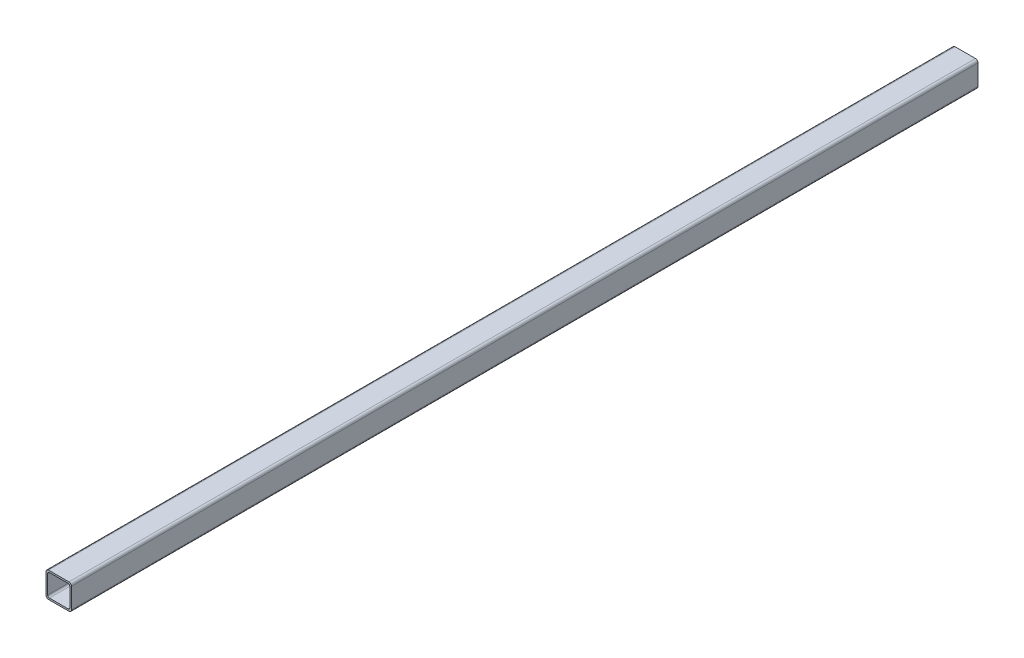
SolidWorks part; units mm, degrees
material "AISI 1020"
ref_plane "Спереди" through (0, 0, 0) normal (0, 0, 1) x (1, 0, 0)
ref_plane "Сверху" through (0, 0, 0) normal (0, 1, 0) x (1, 0, 0)
ref_plane "Справа" through (0, 0, 0) normal (1, 0, 0) x (0, 0, -1)
ref_plane "Плоскость1" through (0, 0, -10) normal (0, 0, 1) x (1, 0, 0)
sketch "Эскиз1" plane through (0, 0, -10) normal (0, 0, 1) x (1, 0, 0)
  line L1 (530.3264, 0) -> (-144.1634, 0) construction
  line B0 (12, 0) -> (-12, 0)
  line B1 (15, 3) -> (15, 27)
  line B2 (12, 30) -> (-12, 30)
  line B3 (-15, 3) -> (-15, 27)
  line B4 (11, 2) -> (-11, 2)
  line B5 (13, 4) -> (13, 26)
  line B6 (11, 28) -> (-11, 28)
  line B7 (-13, 4) -> (-13, 26)
  arc B8 (15, 27) -> (12, 30) centre (12, 27) ccw
  arc B9 (-12, 30) -> (-15, 27) centre (-12, 27) ccw
  arc B10 (-12, 0) -> (-15, 3) centre (-12, 3) cw
  arc B11 (12, 0) -> (15, 3) centre (12, 3) ccw
  arc B12 (13, 26) -> (11, 28) centre (11, 26) ccw
  arc B13 (-11, 28) -> (-13, 26) centre (-11, 26) ccw
  arc B14 (-11, 2) -> (-13, 4) centre (-11, 4) cw
  arc B15 (11, 2) -> (13, 4) centre (11, 4) ccw
sketch_block_instance "Блок-30х30х2-1"
sketch_block "Блок-30х30х2" parameters "D3"=3, "D4"=2, "D1"=30, "D2"=2
extrude "Бобышка-Вытянуть1" add sketch "Эскиз1" against normal offset from surface (534 mm away) 450
mirror "Зеркальное отражение1" about plane through (695.5668, 158.1905, -544) normal (0, 0, 1) of bodies 103
sketch "Эскиз2" plane through (0, 30, 0) normal (0, 1, 0) x (1, 0, 0)
  circle A0 centre (-6, 541.5) radius 5 construction
  circle A1 centre (-6, 541.5) radius 5
extrude "Вырез-Вытянуть1" [suppressed] cut sketch "Эскиз2" against normal through all
